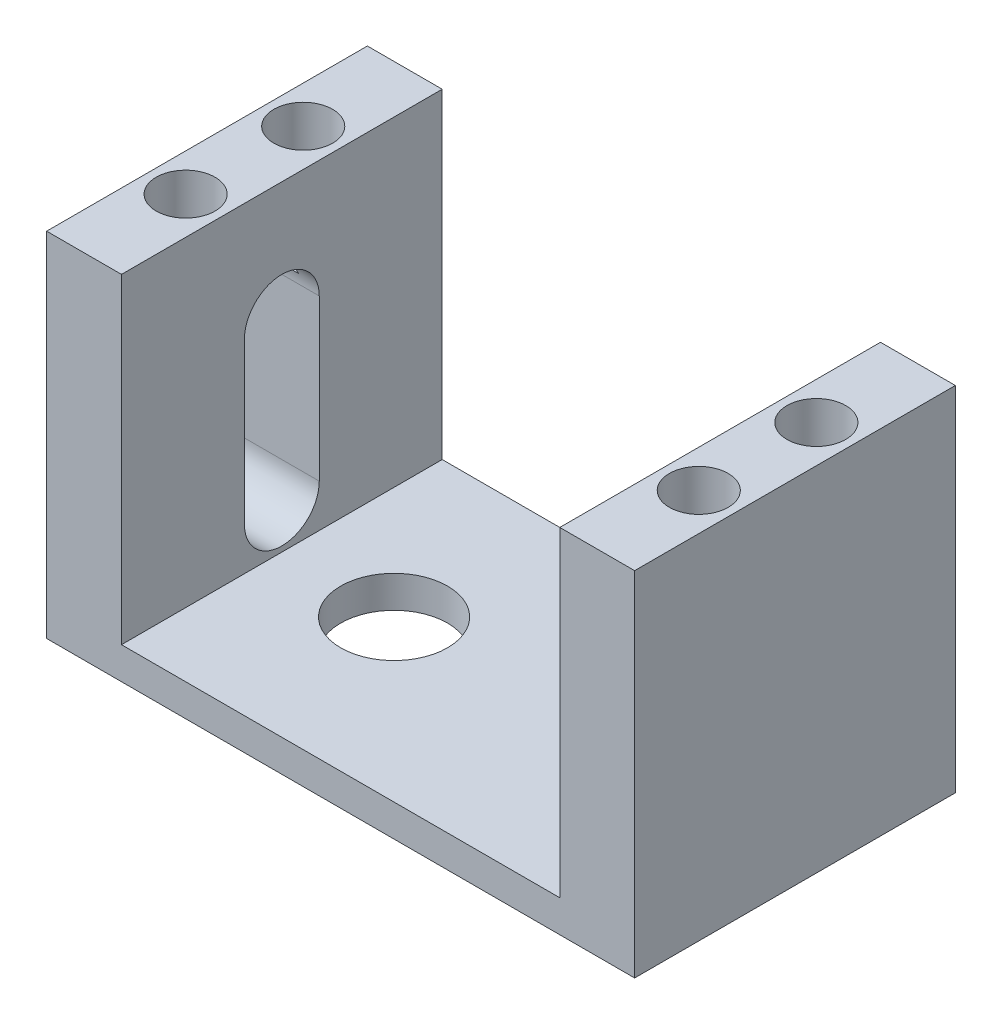
SolidWorks part; units mm, degrees
material "PBT General Purpose"
ref_plane "Front" through (0, 0, 0) normal (0, 0, 1) x (1, 0, 0)
ref_plane "Top" through (0, 0, 0) normal (0, 1, 0) x (1, 0, 0)
ref_plane "Right" through (0, 0, 0) normal (1, 0, 0) x (0, 0, -1)
sketch "Sketch1" plane through (0, 0, 0) normal (0, 1, 0) x (1, 0, 0)
  line L1 (-27.5, 15) -> (27.5, 15)
  line L2 (-27.5, 15) -> (-27.5, -15)
  line L3 (-27.5, -15) -> (27.5, -15)
  line L4 (27.5, 15) -> (27.5, -15)
  line L5 (-27.5, 15) -> (27.5, -15) construction
  line L6 (-27.5, -15) -> (27.5, 15) construction
  point P0 (0, 0)
  dimension "D1" = 30
  dimension "D2" = 55
extrude "Boss-Extrude1" add sketch "Sketch1" along normal blind 3
sketch "Sketch2" plane through (0, 3, 0) normal (0, 1, 0) x (1, 0, 0)
  line L0 (-27.5, -12) -> (-27.5, -15)
  line L1 (-20.5, 15) -> (-20.5, -15)
  line L2 (20.5, -15) -> (27.5, -15)
  line L4 (27.5, -15) -> (27.5, 15)
  line L5 (27.5, 15) -> (-27.5, 15)
  line L6 (-27.5, 15) -> (-27.5, -15)
  line L7 (-27.5, -15) -> (27.5, -15)
  line L8 (27.5, -15) -> (27.5, 15)
  line L9 (27.5, 15) -> (20.5, 15)
  line L10 (-27.5, 15) -> (-27.5, -12)
  line L11 (-27.5, -15) -> (-20.5, -15)
  line L12 (20.5, 15) -> (20.5, -15)
  line L13 (-20.5, 15) -> (-27.5, 15)
  dimension "D3" = 7
  dimension "D2" = 7
  dimension "D1" = 0
extrude "Boss-Extrude2" add sketch "Sketch2" along normal blind 30
sketch "Sketch3" plane through (0, 33, 0) normal (0, 1, 0) x (1, 0, 0)
  line L0 (-24, 5.5) -> (-24, -5.5) construction
  line L1 (-24, -5.5) -> (-24, 0) construction
  line L2 (-24, 0) -> (-27.5, 0) construction
  line L3 (-27.5, 15) -> (-27.5, -15) construction
  line L4 (-20.5, 0) -> (-27.5, 0) construction
  line L5 (-20.5, 15) -> (-20.5, -15) construction
  line L6 (0, 16.7044) -> (0, -24.7895) construction
  circle A0 centre (-24, 5.5) radius 2.75
  circle A1 centre (-24, -5.5) radius 2.75
  circle A2 centre (24, -5.5) radius 2.75
  circle A3 centre (24, 5.5) radius 2.75
  point P9 (-24, 0)
  dimension "D1" = 5.5
  dimension "D2" = 11
extrude "Cut-Extrude1" cut sketch "Sketch3" against normal blind 10
sketch "Sketch4" plane through (-27.5, 0, 0) normal (-1, 0, 0) x (0, 0, 1)
  line L0 (0, 22) -> (0, 7) construction
  line L1 (3.5, 22) -> (3.5, 7)
  line L2 (-3.5, 22) -> (-3.5, 7)
  line L3 (0, 7) -> (0, 0) construction
  line L4 (-15, 0) -> (15, 0) construction
  arc A0 (3.5, 22) -> (-3.5, 22) centre (0, 22) ccw
  arc A1 (-3.5, 7) -> (3.5, 7) centre (0, 7) ccw
  point P3 (0, 14.5)
  dimension "D1" = 7
  dimension "D2" = 7
  dimension "D3" = 15
extrude "Cut-Extrude2" cut sketch "Sketch4" against normal up to next
sketch "Sketch5" plane through (0, 0, 0) normal (0, -1, 0) x (1, 0, 0)
  line L0 (-10, 0) -> (27.5, 0) construction
  line L1 (27.5, 15) -> (27.5, -15) construction
  circle A0 centre (-10, 0) radius 5
  dimension "D2" = 10
  dimension "D1" = 37.5
extrude "Cut-Extrude3" cut sketch "Sketch5" against normal up to next
